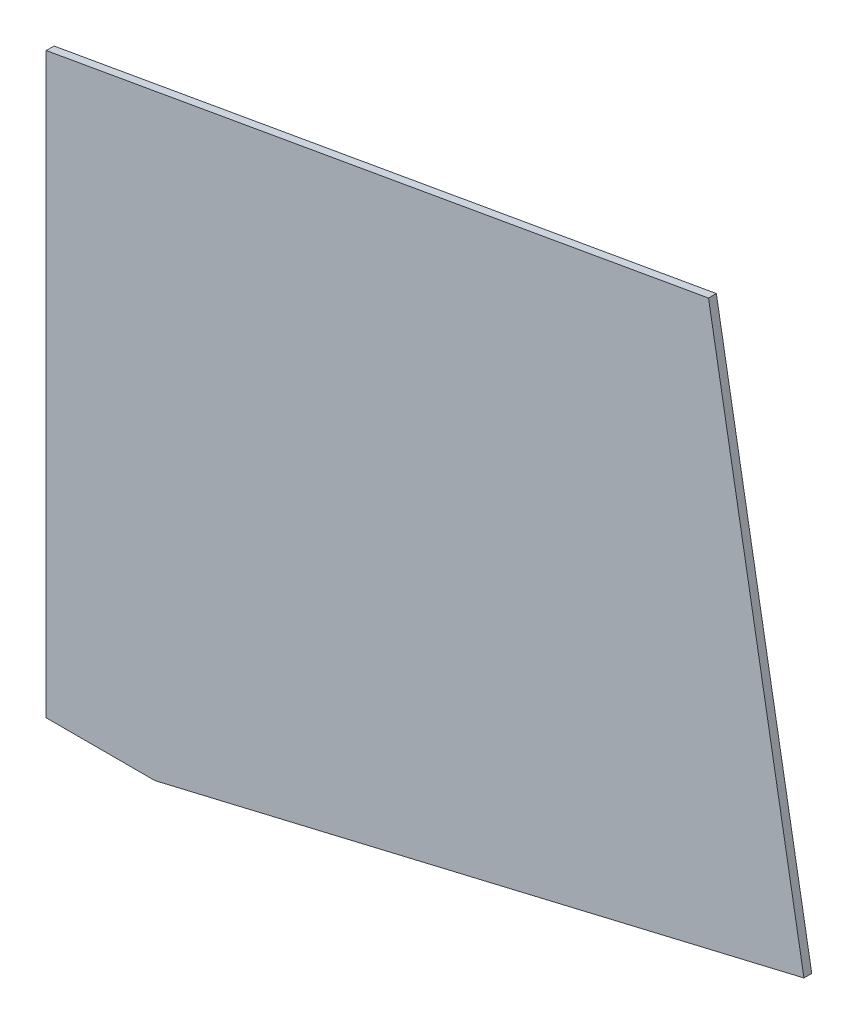
SolidWorks part; units mm, degrees
material "Acrylic (Medium-high impact)"
ref_plane "Front Plane" through (0, 0, 0) normal (0, 0, 1) x (1, 0, 0)
ref_plane "Top Plane" through (0, 0, 0) normal (0, 1, 0) x (1, 0, 0)
ref_plane "Right Plane" through (0, 0, 0) normal (1, 0, 0) x (0, 0, -1)
sketch "Sketch2" plane through (0, 0, 0) normal (0, 0, 1) x (1, 0, 0)
  line L0 (228.9441, 46.4005) -> (32.8676, 0)
  line L1 (0, 0) -> (32.8676, 0)
  line L2 (0, 0) -> (0, 174.625)
  line L3 (0, 174.625) -> (200.1129, 209.9103)
  line L4 (228.9441, 46.4005) -> (200.1129, 209.9103)
  dimension "D1" = 203.2
  dimension "D2" = 100
  dimension "D3" = 174.625
  dimension "D4" = 90
  dimension "D5" = 90
extrude "Boss-Extrude1" add sketch "Sketch2" along normal blind 2.3622
